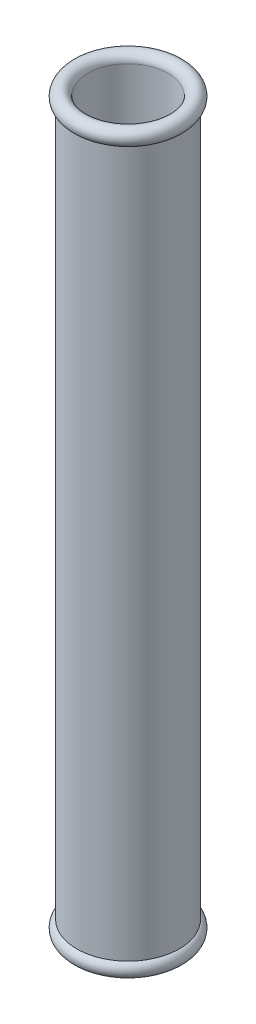
SolidWorks part; units mm, degrees
ref_plane "Front Plane" through (0, 0, 0) normal (0, 0, 1) x (1, 0, 0)
ref_plane "Top Plane" through (0, 0, 0) normal (0, 1, 0) x (1, 0, 0)
ref_plane "Right Plane" through (0, 0, 0) normal (1, 0, 0) x (0, 0, -1)
sketch "Sketch1" plane through (0, 0, 0) normal (0, 0, 1) x (1, 0, 0)
  line L0 (0, 0) -> (0, 50000) construction
  line L1 (1.75, 0) -> (2.25, 0)
  line L2 (1.75, 0) -> (1.75, 31.6)
  line L3 (1.75, 31.6) -> (2.25, 31.6)
  line L4 (2.25, 0) -> (2.25, 31.6)
  circle A0 centre (2.1, 31.6) radius 0.35
  circle A1 centre (2.1, 0) radius 0.35
  dimension "D4" = 0.7
  dimension "D1" = 0.5
  dimension "D2" = 1.75
  dimension "D3" = 31.6
revolve "Revolve2" add sketch "Sketch1" angle 360 about L0
